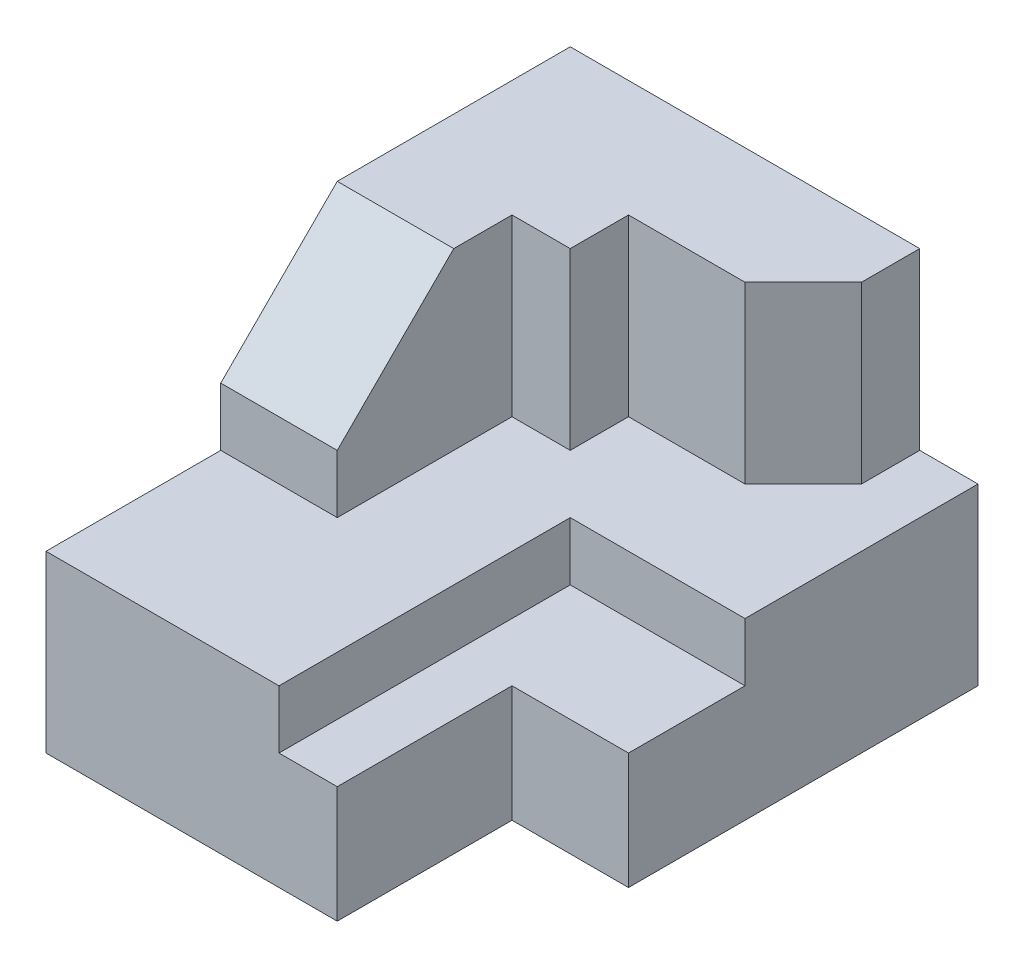
SolidWorks part; units mm, degrees
ref_plane "Front Plane" through (0, 0, 0) normal (0, 0, 1) x (1, 0, 0)
ref_plane "Top Plane" through (0, 0, 0) normal (0, 1, 0) x (1, 0, 0)
ref_plane "Right Plane" through (0, 0, 0) normal (1, 0, 0) x (0, 0, -1)
sketch "Sketch1" plane through (0, 0, 0) normal (0, 0, 1) x (1, 0, 0)
  line L1 (3.5, -3) -> (-3.5, -3)
  line L2 (3.5, -3) -> (3.5, 3)
  line L3 (3.5, 3) -> (-3.5, 3)
  line L4 (-3.5, -3) -> (-3.5, 3)
  line L5 (3.5, -3) -> (-3.5, 3) construction
  line L6 (3.5, 3) -> (-3.5, -3) construction
  point P0 (0, 0)
  dimension "D1" = 6
  dimension "D2" = 7
extrude "Boss-Extrude1" add sketch "Sketch1" along normal blind 9
sketch "Sketch2" plane through (0, 3, 0) normal (0, 1, 0) x (1, 0, 0)
  line L0 (2.5, 0) -> (2.5, -1)
  line L1 (3.5, 0) -> (-3.5, 0) construction
  line L2 (2.5, -1) -> (1.5, -2)
  line L3 (1.5, -2) -> (-0.5, -2)
  line L4 (-0.5, -2) -> (-0.5, -3)
  line L5 (-0.5, -3) -> (-1.5, -3)
  line L6 (-1.5, -3) -> (-1.5, -6)
  line L7 (-1.5, -6) -> (-3.5, -6)
  line L8 (-3.5, -9) -> (-3.5, 0) construction
  line L9 (-3.5, -6) -> (-3.5, 0)
  line L10 (-3.5, 0) -> (2.5, 0)
  dimension "D1" = 1
  dimension "D2" = 1
  dimension "D3" = 2
  dimension "D4" = 1
  dimension "D5" = 1
  dimension "D6" = 3
  dimension "D7" = 2
  dimension "D8" = 3
extrude "Cut-Extrude1" cut sketch "Sketch2" against normal blind 3 flip side to cut
sketch "Sketch3" plane through (0, 0, 0) normal (0, 1, 0) x (1, 0, 0)
  line L0 (3.5, -4) -> (0.5, -4)
  line L1 (3.5, -9) -> (3.5, 0) construction
  line L2 (0.5, -4) -> (0.5, -9)
  line L3 (3.5, -9) -> (-3.5, -9) construction
  line L4 (0.5, -9) -> (3.5, -9)
  line L5 (3.5, -9) -> (3.5, -4)
  dimension "D1" = 3
  dimension "D2" = 5
extrude "Cut-Extrude2" cut sketch "Sketch3" against normal blind 1
sketch "Sketch4" plane through (0, -1, 0) normal (0, 1, 0) x (1, 0, 0)
  line L0 (3.5, -9) -> (3.5, -6)
  line L1 (3.5, -9) -> (3.5, -4) construction
  line L2 (3.5, -6) -> (1.5, -6)
  line L3 (1.5, -6) -> (1.5, -9)
  line L4 (0.5, -9) -> (3.5, -9) construction
  line L5 (1.5, -9) -> (3.5, -9)
  dimension "D1" = 2
  dimension "D2" = 3
extrude "Cut-Extrude3" cut sketch "Sketch4" against normal blind 2
sketch "Sketch5" plane through (-1.5, 0, 0) normal (1, 0, 0) x (0, 0, -1)
  line L0 (-4, 3) -> (-6, 1)
  line L1 (-6, 3) -> (-3, 3) construction
  line L2 (-6, 0) -> (-6, 3) construction
  line L3 (-6, 1) -> (-6, 3)
  line L4 (-6, 3) -> (-4, 3)
  dimension "D1" = 1
  dimension "D2" = 1
extrude "Cut-Extrude4" cut sketch "Sketch5" against normal blind 2
